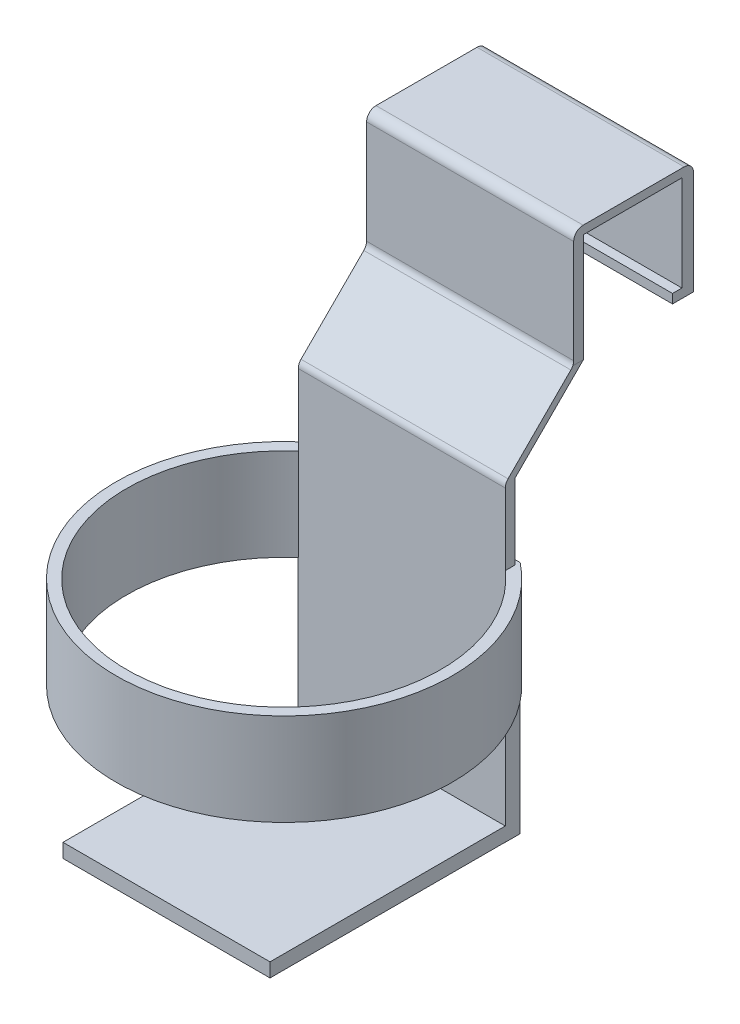
SolidWorks part; units mm, degrees
other "Markup1"
sketch "Sketch10" plane through (0, -96.9017, 111.153) normal (-0.2214, -0.0171, 0.975) x (0.9752, -0.0018, 0.2214)
ref_plane "Front Plane" through (0, 0, 0) normal (0, 0, 1) x (1, 0, 0)
ref_plane "Top Plane" through (0, 0, 0) normal (0, 1, 0) x (1, 0, 0)
ref_plane "Right Plane" through (0, 0, 0) normal (1, 0, 0) x (0, 0, -1)
sketch "Sketch2" plane through (0, 0, 0) normal (0, 1, 0) x (1, 0, 0)
  line L1 (0, 0) -> (55.9018, 0)
  line L2 (0, 0) -> (0, 3.1373)
  line L3 (0, 3.1373) -> (55.9018, 3.1373)
  line L4 (55.9018, 0) -> (55.9018, 3.1373)
extrude "Boss-Extrude1" add sketch "Sketch2" along normal blind 36.83 contours L3 L4 L1 L2
sketch "Sketch3" plane through (0, 0, 0) normal (0, 0, 1) x (1, 0, 0)
  line L0 (55.9018, 36.83) -> (55.9018, 0) construction
  line L1 (0, 36.83) -> (55.9018, 36.83)
  line L2 (0, 36.83) -> (0, 34.5713)
  line L3 (0, 34.5713) -> (55.9018, 34.5713)
  line L4 (55.9018, 36.83) -> (55.9018, 34.5713)
extrude "Boss-Extrude2" add sketch "Sketch3" along normal blind 29.21
sketch "Sketch4" plane through (0, 34.5713, 0) normal (0, -1, 0) x (1, 0, 0)
  line L0 (55.9018, 29.21) -> (55.9018, 0) construction
  line L1 (0, 29.21) -> (55.9018, 29.21)
  line L2 (0, 29.21) -> (0, 26.5535)
  line L3 (0, 26.5535) -> (55.9018, 26.5535)
  line L4 (55.9018, 29.21) -> (55.9018, 26.5535)
extrude "Boss-Extrude3" add sketch "Sketch4" along normal blind 29.21
sketch "Sketch6" plane through (0, 0, 0) normal (-1, 0, 0) x (0, 0, 1)
  line L0 (29.21, 5.3613) -> (29.21, 8.9328)
  line L1 (29.21, 36.83) -> (29.21, 5.3613) construction
  line L2 (29.21, 5.3613) -> (47.653, -13.0817)
  line L3 (47.653, -13.0817) -> (44.9965, -13.0817)
  line L4 (44.9965, -13.0817) -> (26.5535, 5.3613)
  line L5 (44.9965, -13.0817) -> (27.6754, -13.0817) construction
  line L14 (-3.1373, 0) -> (0, 0)
  line L15 (0, 0) -> (0, 34.5713)
  line L16 (0, 34.5713) -> (26.5535, 34.5713)
  line L17 (26.5535, 34.5713) -> (26.5535, 5.3613)
  line L18 (26.5535, 5.3613) -> (29.21, 5.3613)
  line L19 (29.21, 5.3613) -> (29.21, 36.83)
  line L20 (29.21, 36.83) -> (-3.1373, 36.83)
  line L21 (-3.1373, 36.83) -> (-3.1373, 0)
  line L22 (-3.1373, 0) -> (0, 0)
  line L23 (0, 0) -> (0, 34.5713)
  line L24 (0, 34.5713) -> (26.5535, 34.5713)
  line L25 (26.5535, 34.5713) -> (26.5535, 5.3613)
  line L27 (29.21, 8.9328) -> (29.21, 36.83)
  line L28 (29.21, 36.83) -> (-3.1373, 36.83)
  line L29 (-3.1373, 36.83) -> (-3.1373, 0)
  dimension "D1" = 45
  dimension "D2" = 45
  dimension "D3" = 0
extrude "Boss-Extrude4" add sketch "Sketch6" against normal blind 55.88
sketch "Sketch7" plane through (0, -13.0817, 0) normal (0, -1, 0) x (1, 0, 0)
  line L0 (55.88, 44.9965) -> (55.88, 47.653) construction
  line L1 (0, 44.9965) -> (55.88, 44.9965)
  line L2 (0, 44.9965) -> (0, 47.653)
  line L3 (0, 47.653) -> (55.88, 47.653)
  line L4 (55.88, 44.9965) -> (55.88, 47.653)
  line L5 (55.88, 47.653) -> (0, 47.653) construction
extrude "Boss-Extrude5" add sketch "Sketch7" along normal blind 83.82
sketch "Sketch8" plane through (0, 0, 47.653) normal (0, 0, 1) x (1, 0, 0)
  line L0 (55.88, -96.9017) -> (55.88, -13.0817) construction
  line L1 (0, -96.9017) -> (55.88, -96.9017)
  line L2 (0, -96.9017) -> (0, -93.1233)
  line L3 (0, -93.1233) -> (55.88, -93.1233)
  line L4 (55.88, -96.9017) -> (55.88, -93.1233)
extrude "Boss-Extrude6" add sketch "Sketch8" along normal blind 63.5
sketch "Sketch18" plane through (0, 0, 0) normal (0, 0, 1) x (1, 0, 0)
  line L0 (55.9018, 34.5713) -> (55.9018, 0) construction
  line L1 (0, 0) -> (55.9018, 0)
  line L2 (0, 0) -> (0, 2.4133)
  line L3 (0, 2.4133) -> (55.9018, 2.4133)
  line L4 (55.9018, 0) -> (55.9018, 2.4133)
extrude "Boss-Extrude9" add sketch "Sketch18" along normal blind 3.81
sketch "Sketch20" plane through (0, -93.1233, 0) normal (0, 1, 0) x (1, 0, 0)
  line L0 (27.94, -111.153) -> (27.94, -47.653) construction
  line L3 (55.88, -111.153) -> (0, -111.153) construction
  line L4 (55.88, -47.653) -> (0, -47.653) construction
  circle A0 centre (27.94, -79.403) radius 45.3659
  point P3 (27.94, -111.153)
extrude "Boss-Extrude10" add sketch "Sketch20" along normal blind 59.69
sketch "Sketch21" plane through (0, -33.4333, 0) normal (0, 1, 0) x (1, 0, 0)
  line L1 (55.88, -47.653) -> (0, -47.653)
  arc A1 (0, -47.653) -> (55.88, -47.653) centre (27.94, -79.5154) ccw
extrude "Cut-Extrude2" cut sketch "Sketch21" against normal blind 59.69
sketch "Sketch22" plane through (0, -33.4333, 0) normal (0, 1, 0) x (1, 0, 0)
  line L0 (-0.1123, -43.7499) -> (55.9923, -43.7499)
  line L1 (-0.1123, -43.7499) -> (-0.1123, -30.8275)
  line L2 (-0.1123, -30.8275) -> (52.4857, -29.8796)
  line L3 (52.4857, -29.8796) -> (55.9923, -43.7499)
  circle A0 centre (27.94, -79.403) radius 45.3659 construction
extrude "Cut-Extrude4" cut sketch "Sketch22" against normal blind 59.69 contours L2 L3 L0 L1
sketch "Sketch23" plane through (0, -93.1233, 0) normal (0, -1, 0) x (1, 0, 0)
  line L0 (27.94, 43.7499) -> (27.94, 124.7689) construction
  line L1 (-0.1123, 43.7499) -> (55.9923, 43.7499) construction
  arc A0 (55.9923, 43.7499) -> (-0.1123, 43.7499) centre (27.94, 79.403) ccw construction
  circle A1 centre (27.94, 84.2594) radius 50.6198
extrude "Cut-Extrude5" cut sketch "Sketch23" against normal blind 34.798
sketch "Sketch24" plane through (0, -58.3253, 0) normal (0, -1, 0) x (1, 0, 0)
  line L1 (-0.1123, 43.7499) -> (55.88, 43.7499)
  line L2 (-0.1123, 43.7499) -> (-0.1123, 47.653)
  line L3 (-0.1123, 47.653) -> (55.88, 47.653)
  line L4 (55.88, 43.7499) -> (55.88, 47.653)
extrude "Boss-Extrude11" add sketch "Sketch24" along normal blind 38.608
sketch "Sketch25" plane through (0, 0, 0) normal (0, -1, 0) x (1, 0, 0)
  line L0 (0, 3.81) -> (55.9018, 3.81) construction
  line L1 (55.9018, 3.81) -> (0, 3.81)
  line L2 (55.9018, 3.81) -> (55.9018, -3.1373)
  line L3 (55.9018, -3.1373) -> (0, -3.1373)
  line L4 (0, 3.81) -> (0, -3.1373)
extrude "Cut-Extrude6" cut sketch "Sketch25" against normal blind 6.35
sketch "Sketch26" plane through (0, 0, 0) normal (0, 0, 1) x (1, 0, 0)
  line L0 (0, 34.5713) -> (0, 6.35) construction
  line L1 (55.9018, 6.35) -> (0, 6.35)
  line L2 (55.9018, 6.35) -> (55.9018, 8.8108)
  line L3 (55.9018, 8.8108) -> (0, 8.8108)
  line L4 (0, 6.35) -> (0, 8.8108)
extrude "Boss-Extrude12" add sketch "Sketch26" along normal blind 2.54
fillet "Fillet2" radius 2.54 2 edges at (27.9509, 36.83, 29.21) (27.9509, 36.83, -3.1373)
fillet "Fillet4" radius 2.54 1 edges at (27.94, 5.3613, 29.21)
fillet "Fillet5" radius 2.54 1 edges at (27.94, -13.0817, 47.653)
